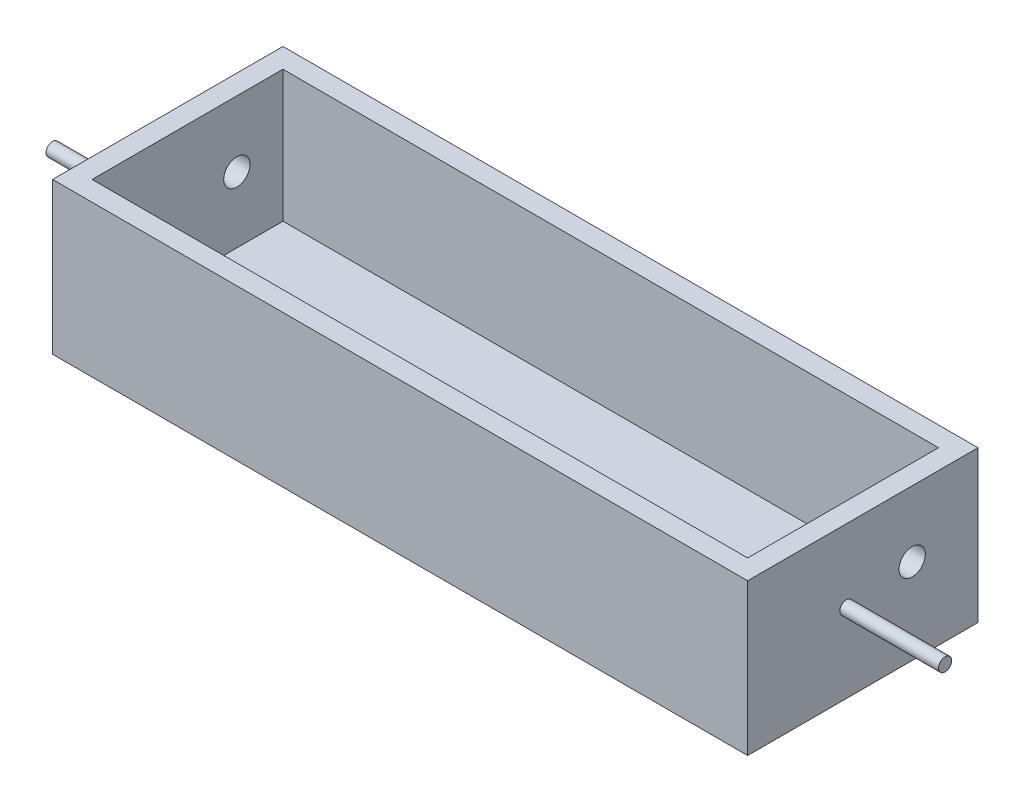
SolidWorks part; units mm, degrees
ref_plane "前视基准面" through (0, 0, 0) normal (0, 0, 1) x (1, 0, 0)
ref_plane "上视基准面" through (0, 0, 0) normal (0, 1, 0) x (1, 0, 0)
ref_plane "右视基准面" through (0, 0, 0) normal (1, 0, 0) x (0, 0, -1)
sketch "草图1" plane through (0, 0, 0) normal (0, 1, 0) x (1, 0, 0)
  line L0 (-52.8, 0) -> (-37.5, 0)
  line L1 (-52.8, -10) -> (52.8, -10)
  line L2 (-52.8, -10) -> (-52.8, 10)
  line L3 (-52.8, 10) -> (52.8, 10)
  line L4 (52.8, -10) -> (52.8, 10)
  line L5 (-52.8, -10) -> (52.8, 10) construction
  line L6 (-52.8, 10) -> (52.8, -10) construction
  line L7 (52.8, 0) -> (37.5, 0)
  circle A0 centre (-37.5, 0) radius 4
  circle A1 centre (37.5, 0) radius 4
  point P0 (0, 0)
  dimension "D1" = 105.6
  dimension "D2" = 20
extrude "凸台-拉伸1" add sketch "草图1" along normal blind 3
sketch "草图10" plane through (0, 3, 0) normal (0, 1, 0) x (1, 0, 0)
  line L1 (-52.8, -10) -> (52.8, -10)
  line L2 (-52.8, -10) -> (-52.8, 10)
  line L3 (-52.8, 10) -> (52.8, 10)
  line L4 (52.8, -10) -> (52.8, 10)
  line L5 (-52.8, -10) -> (52.8, 10) construction
  line L6 (-52.8, 10) -> (52.8, -10) construction
  line L7 (-49.8, -7) -> (49.8, -7)
  line L8 (-49.8, -7) -> (-49.8, 7)
  line L9 (-49.8, 7) -> (49.8, 7)
  line L10 (49.8, -7) -> (49.8, 7)
  line L11 (-49.8, -7) -> (49.8, 7) construction
  line L12 (-49.8, 7) -> (49.8, -7) construction
  point P0 (0, 0)
  point P7 (0, 0)
extrude "凸台-拉伸2" add sketch "草图10" along normal blind 20
sketch "草图11" plane through (-52.8, 0, 0) normal (-1, 0, 0) x (0, 0, 1)
  line L0 (0, 23) -> (0, 13)
  line L1 (-10, 23) -> (10, 23) construction
  circle A0 centre (0, 13) radius 2
extrude "切除-拉伸1" cut sketch "草图11" against normal blind 110
sketch "草图12" plane through (-52.8, 0, 0) normal (-1, 0, 0) x (0, 0, 1)
  line L1 (10, 0) -> (25, 0)
  line L2 (10, 0) -> (10, 23)
  line L3 (10, 23) -> (25, 23)
  line L4 (25, 0) -> (25, 23)
  line L5 (10, 0) -> (25, 23) construction
  line L6 (10, 23) -> (25, 0) construction
  point P4 (17.5, 11.5)
extrude "凸台-拉伸3" add sketch "草图12" against normal blind 105.6
sketch "草图14" plane through (0, 23, 0) normal (0, 1, 0) x (1, 0, 0)
  line L2 (-49.8, 7) -> (-49.8, -25)
  line L4 (52.8, -25) -> (-52.8, -25) construction
  line L5 (-49.8, -25) -> (-49.8, -22)
  line L6 (-49.8, -22) -> (49.8, -22)
  line L7 (49.8, -22) -> (49.8, -7)
  line L8 (49.8, -7) -> (-49.8, -7)
  line M6 (49.8, -7) -> (-49.8, -7)
extrude "切除-拉伸2" cut sketch "草图14" against normal blind 20 contours L6 L7 L2 M6
sketch "草图16" plane through (0, 0, 0) normal (0, -1, 0) x (1, 0, 0)
  line L0 (-52.8, 25) -> (-37.5, 25)
  line L1 (52.8, 25) -> (-52.8, 25) construction
  line L2 (-37.5, 25) -> (-37.5, -9.5603)
  line L3 (52.8, 25) -> (37.5, 25)
  line L4 (37.5, 25) -> (37.5, -10)
  line L5 (-52.8, -10) -> (52.8, -10) construction
  circle A0 centre (-37.5, 7.7199) radius 4
  circle A1 centre (37.5, 7.5) radius 4
extrude "切除-拉伸3" cut sketch "草图16" against normal blind 20 contours L2 A0 | L2 A0 | L4 A1 | L4 A1
sketch "草图17" plane through (-52.8, 0, 0) normal (-1, 0, 0) x (0, 0, 1)
  line L0 (0, 13) -> (25, 13)
  line L1 (25, 0) -> (25, 23) construction
  line L2 (0, 13) -> (10, 13)
  circle A0 centre (10, 12) radius 1
extrude "凸台-拉伸4" add sketch "草图17" along normal blind 15 and the other way blind 120.6 contours A0
sketch "草图19" plane through (0, 3, 0) normal (0, 1, 0) x (1, 0, 0)
  line L1 (-49.8, 7) -> (49.8, 7)
  line L2 (-49.8, 7) -> (-49.8, -22)
  line L3 (-49.8, -22) -> (49.8, -22)
  line L4 (49.8, 7) -> (49.8, -22)
extrude "切除-拉伸4" cut sketch "草图19" along normal blind 10
